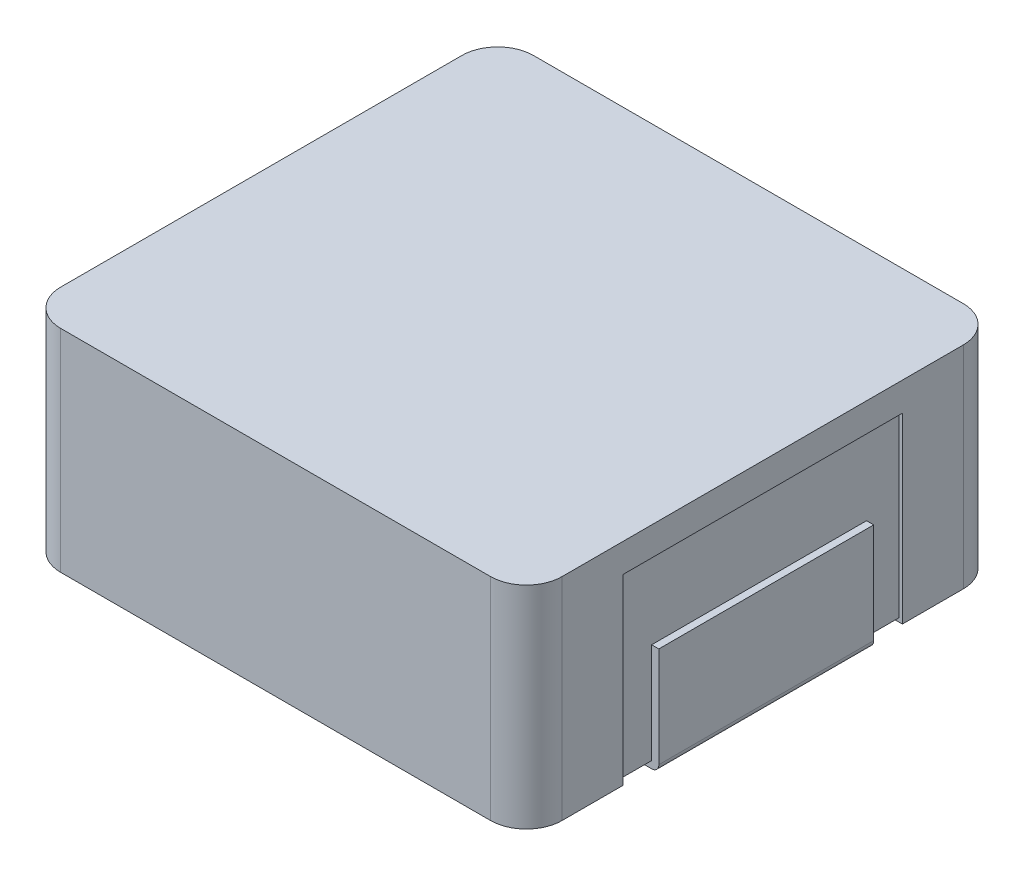
SolidWorks part; units mm, degrees
ref_plane "前视基准面" through (0, 0, 0) normal (0, 0, 1) x (1, 0, 0)
ref_plane "上视基准面" through (0, 0, 0) normal (0, 1, 0) x (1, 0, 0)
ref_plane "右视基准面" through (0, 0, 0) normal (1, 0, 0) x (0, 0, -1)
other "Configuration Table"
sketch "草图1" plane through (0, 0, 0) normal (0, 1, 0) x (1, 0, 0)
  line L1 (-3, -3.3) -> (3, -3.3)
  line L2 (-3.5, -2.8) -> (-3.5, 2.8)
  line L3 (-3, 3.3) -> (3, 3.3)
  line L4 (3.5, -2.8) -> (3.5, 2.8)
  line L5 (-3.5, -3.3) -> (3.5, 3.3) construction
  line L6 (-3.5, 3.3) -> (3.5, -3.3) construction
  arc A0 (-3, -3.3) -> (-3.5, -2.8) centre (-3, -2.8) cw
  arc A1 (3, -3.3) -> (3.5, -2.8) centre (3, -2.8) ccw
  arc A2 (3, 3.3) -> (3.5, 2.8) centre (3, 2.8) cw
  arc A3 (-3.5, 2.8) -> (-3, 3.3) centre (-3, 2.8) cw
  point P0 (0, 0)
  dimension "圆角半径" = 0.5
  dimension "长度" = 6.6
  dimension "宽度(实际长度-0.1用于放置引脚)" = 7
extrude "凸台-拉伸1" add sketch "草图1" along normal blind 2.95
sketch "草图2" plane through (0, 0, 0) normal (0, -1, 0) x (1, 0, 0)
  line L0 (-3.5, -2.8) -> (-3.5, 2.8) construction
  line L1 (3.5, 2.8) -> (3.5, -2.8) construction
  line L3 (-3.5, 1.95) -> (-0.95, 1.95)
  line L4 (-3.5, 1.95) -> (-3.5, -1.95)
  line L5 (-3.5, -1.95) -> (-0.95, -1.95)
  line L6 (-0.95, 1.95) -> (-0.95, -1.95)
  line L7 (3.5, 1.95) -> (0.95, 1.95)
  line L8 (3.5, 1.95) -> (3.5, -1.95)
  line L9 (3.5, -1.95) -> (0.95, -1.95)
  line L10 (0.95, 1.95) -> (0.95, -1.95)
  point P0 (-3.5, 0)
  point P1 (3.5, 0)
  dimension "底面凹坑长" = 3.9
  dimension "底面凹坑宽" = 2.55
extrude "切除-拉伸1" cut sketch "草图2" against normal blind 0.05
sketch "草图3" plane through (0, 0.05, 0) normal (0, -1, 0) x (1, 0, 0)
  line L1 (-3.5, -1.95) -> (-0.95, -1.95) construction
  point P0 (-2.6, -1.5)
  dimension "引脚边缘开始延申处与比凹坑边缘距离" = 0.45
ref_plane "基准面1" through (0, 0, -1.5) normal (0, 0, -1) x (-1, 0, 0)
sketch "草图6" plane through (-3.5, 0, 0) normal (-1, 0, 0) x (0, 0, 1)
  line L1 (-1.95, 0) -> (1.95, 0)
  line L2 (-1.95, 0) -> (-1.95, 2.55)
  line L3 (-1.95, 2.55) -> (1.95, 2.55)
  line L4 (1.95, 0) -> (1.95, 2.55)
  dimension "侧面凹坑高" = 2.55
extrude "切除-拉伸3" cut sketch "草图6" against normal blind 0.05
sketch "草图8" plane through (0, 0, -1.5) normal (0, 0, -1) x (-1, 0, 0)
  line L0 (2.05, 0.05) -> (2.05, -0.05)
  line L1 (2.05, -0.05) -> (3.45, -0.05)
  line L2 (3.55, 0.05) -> (3.55, 1.45)
  line L3 (3.55, 1.45) -> (3.45, 1.45)
  line L4 (3.45, 1.45) -> (3.45, 0.05)
  line L5 (3.45, 0.05) -> (2.05, 0.05)
  line L6 (3.45, 0.05) -> (0.95, 0.05) construction
  line L7 (3.45, 0.05) -> (3.45, 2.55) construction
  arc A0 (3.45, -0.05) -> (3.55, 0.05) centre (3.45, 0.05) ccw
  point P12 (3.55, -0.05)
  dimension "引脚弯曲处圆角半径" = 0.1
  dimension "引脚厚度" = 0.1
  dimension "引脚底面宽度D" = 1.5
extrude "凸台-拉伸3" add sketch "草图8" against normal blind 3 separate body
ref_plane "基准面4" through (0, 0, 0) normal (-1, 0, 0) x (0, 0, 1)
mirror "镜向3" about plane through (0, 0, 0) normal (-1, 0, 0) of "切除-拉伸3"
mirror "镜向4" about plane through (0, 0, 0) normal (-1, 0, 0) of "凸台-拉伸3"
equation "\"侧面凹坑高@草图6\"= \"底面凹坑宽@草图2\"'应当和底面的相等"
equation "\"底面凹坑宽@草图2\"= \"引脚底面宽度D@草图8\" * 1.7'没有固定的数值，选了个看着顺眼的倍数，总之比引脚大一圈"
equation "\"底面凹坑长@草图2\" = \"引脚总宽度E@凸台-拉伸3\" * 1.3'没有固定的数值，选了个看着顺眼的倍数，总之比引脚大一圈"
equation "\"引脚边缘开始延申处与比凹坑边缘距离@草图3\"= ( \"底面凹坑长@草图2\" - \"引脚总宽度E@凸台-拉伸3\" ) / 2mm'计算结果是引脚在凹坑中心的位置"
